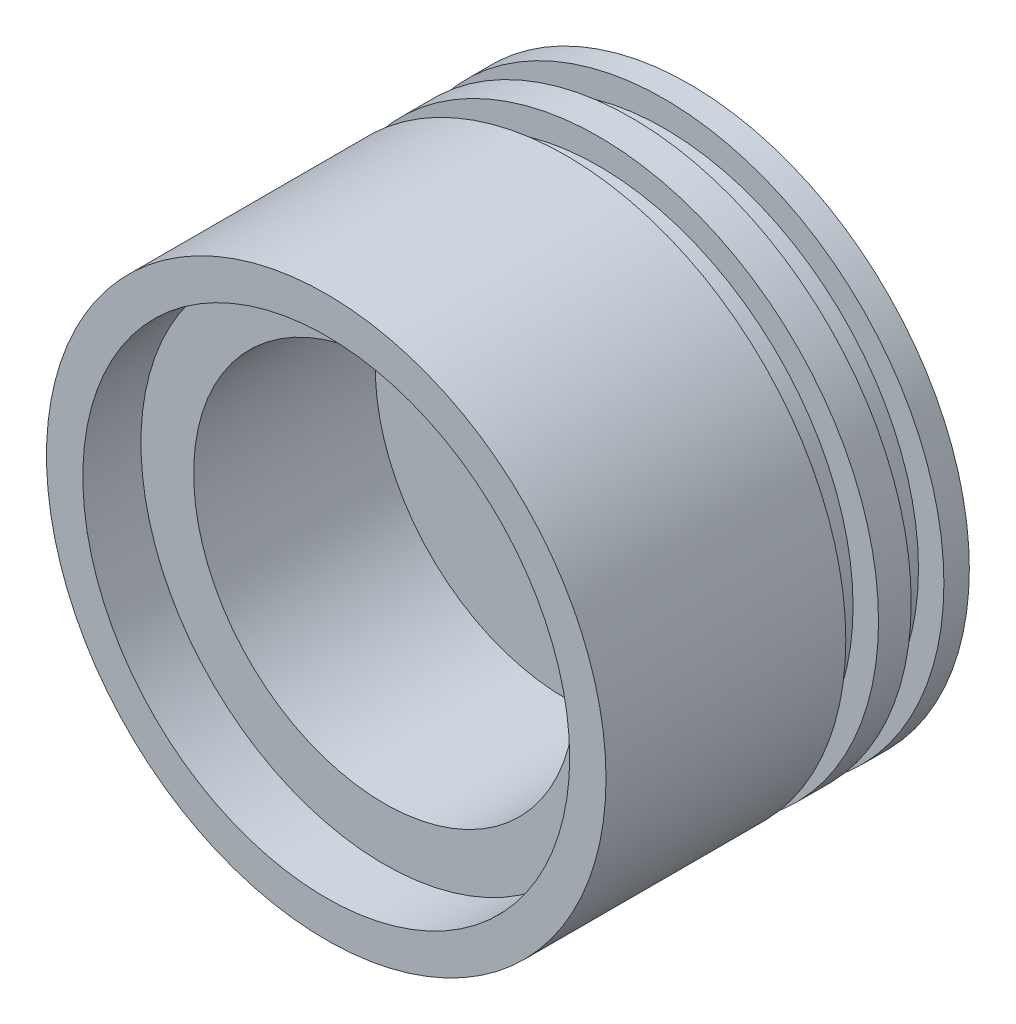
SolidWorks part; units mm, degrees
ref_plane "Front Plane" through (0, 0, 0) normal (0, 0, 1) x (1, 0, 0)
ref_plane "Top Plane" through (0, 0, 0) normal (0, 1, 0) x (1, 0, 0)
ref_plane "Right Plane" through (0, 0, 0) normal (1, 0, 0) x (0, 0, -1)
sketch "Sketch1" plane through (0, 0, 0) normal (0, 1, 0) x (1, 0, 0)
  line L0 (0, -14.1933) -> (0, 122.24) construction
  line L1 (0, 66) -> (0, 110)
  line L2 (0, 66) -> (52.5, 66)
  line L3 (52.5, 66) -> (52.5, 16)
  line L4 (52.5, 16) -> (67, 16)
  line L5 (67, 16) -> (67, 0)
  line L6 (67, 0) -> (77, 0)
  line L7 (77, 0) -> (77, 66)
  line L8 (77, 66) -> (70, 66)
  line L9 (70, 66) -> (70, 75)
  line L10 (70, 75) -> (77, 75)
  line L11 (77, 75) -> (77, 84)
  line L12 (77, 84) -> (70, 84)
  line L13 (70, 84) -> (70, 93)
  line L14 (70, 93) -> (77, 93)
  line L15 (77, 100) -> (77, 93)
  arc A0 (0, 110) -> (77, 100) centre (0, -191.45) cw
  dimension "D3" = 85
  dimension "D6" = 10
  dimension "D9" = 105
  dimension "D1" = 110
  dimension "D2" = 94
  dimension "D4" = 58
  dimension "D5" = 110
  dimension "D7" = 136.5009
  dimension "D8" = 50
  dimension "D10" = 140
  dimension "D11" = 7
revolve "Revolve7" add sketch "Sketch1" angle 360 about L0
